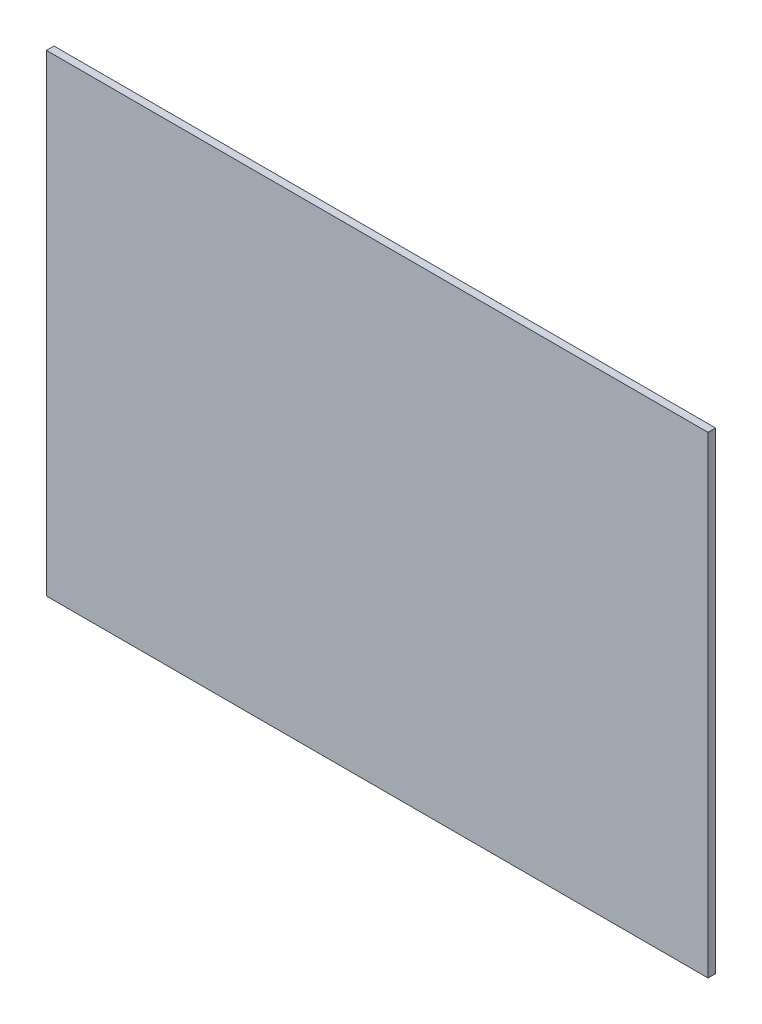
SolidWorks part; units mm, degrees
ref_plane "Front Plane" through (0, 0, 0) normal (0, 0, 1) x (1, 0, 0)
ref_plane "Top Plane" through (0, 0, 0) normal (0, 1, 0) x (1, 0, 0)
ref_plane "Right Plane" through (0, 0, 0) normal (1, 0, 0) x (0, 0, -1)
sketch "Sketch1" plane through (0, 0, 0) normal (0, 0, 1) x (1, 0, 0)
  line L1 (700, 500) -> (0, 500)
  line L2 (700, 500) -> (700, 0)
  line L3 (700, 0) -> (0, 0)
  line L4 (0, 500) -> (0, 0)
  dimension "D1" = 500
  dimension "D2" = 700
extrude "Boss-Extrude1" add sketch "Sketch1" along normal blind 8
